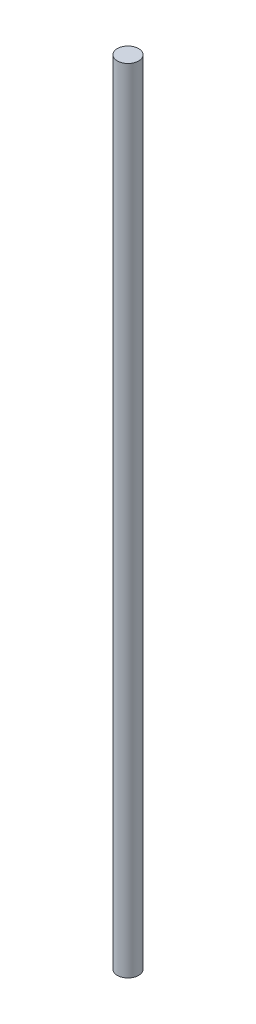
SolidWorks part; units mm, degrees
ref_plane "Plan de face" through (0, 0, 0) normal (0, 0, 1) x (1, 0, 0)
ref_plane "Plan de dessus" through (0, 0, 0) normal (0, 1, 0) x (1, 0, 0)
ref_plane "Plan de droite" through (0, 0, 0) normal (1, 0, 0) x (0, 0, -1)
sketch "Esquisse1" plane through (0, 0, 0) normal (0, 1, 0) x (1, 0, 0)
  circle A0 centre (0, 0) radius 1.5
  dimension "D1" = 3
extrude "Boss.-Extru.1" add sketch "Esquisse1" along normal blind 111
